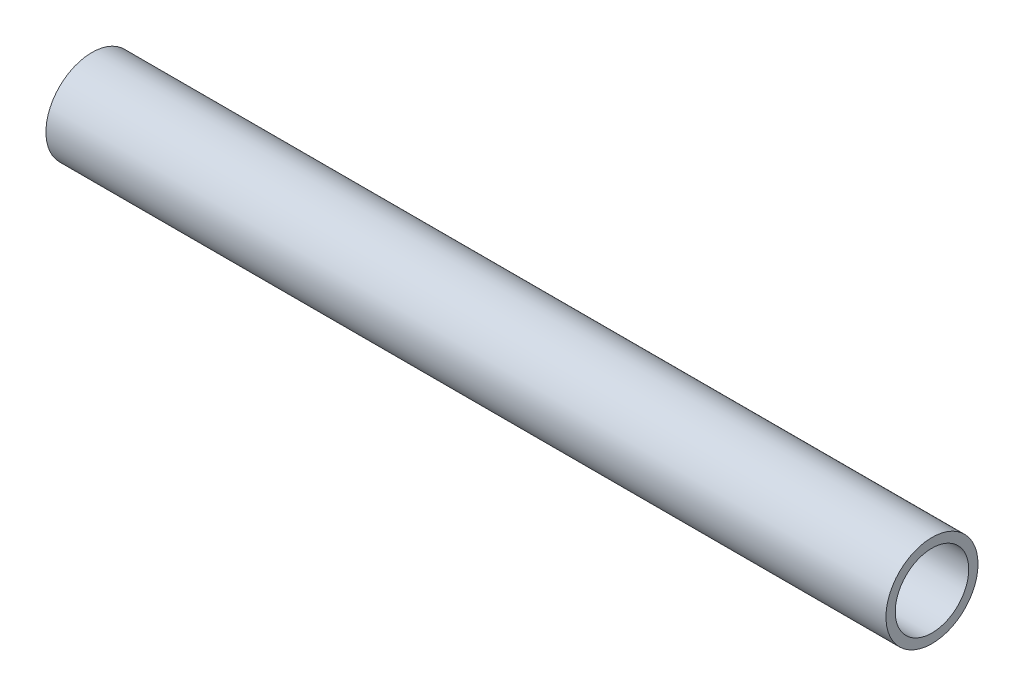
SolidWorks part; units mm, degrees
ref_plane "Front Plane" through (0, 0, 0) normal (0, 0, 1) x (1, 0, 0)
ref_plane "Top Plane" through (0, 0, 0) normal (0, 1, 0) x (1, 0, 0)
ref_plane "Right Plane" through (0, 0, 0) normal (1, 0, 0) x (0, 0, -1)
sketch "Sketch1" plane through (0, 0, 0) normal (1, 0, 0) x (0, 0, -1)
  circle A0 centre (0, 0) radius 16.7005
  circle A1 centre (0, 0) radius 13.335
  dimension "D1" = 33.401
  dimension "D2" = 26.67
extrude "Boss-Extrude1" add sketch "Sketch1" along normal blind 304.8
hole_wizard "1/4-28 Tapped Hole1" [suppressed] positions "3DSketch2" profile "Sketch3" tap size "1/4-28" standard "ANSI Inch"
sketch3d "3DSketch2"
  point P0 (152.4, 0, 16.7005)
sketch "Sketch3" plane through (152.4, 0, 16.7005) normal (1, 0, 0) x (0, -1, 0)
  line L0 (0, 0) -> (0, 3.3655)
  line L1 (0, 3.3655) -> (2.7051, 3.3655)
  line L2 (2.7051, 3.3655) -> (2.7051, 0)
  line L5 (2.7051, 0) -> (0, 0)
  line L11 (0, -6.35) -> (0, 107.95) construction
  dimension "Thru Tap Drill Dia." = 5.4102
  dimension "Thru Tap Drill Depth" = 3.3655
cosmetic thread "Hole Thread1" [suppressed] parameters "D2"=6.35
